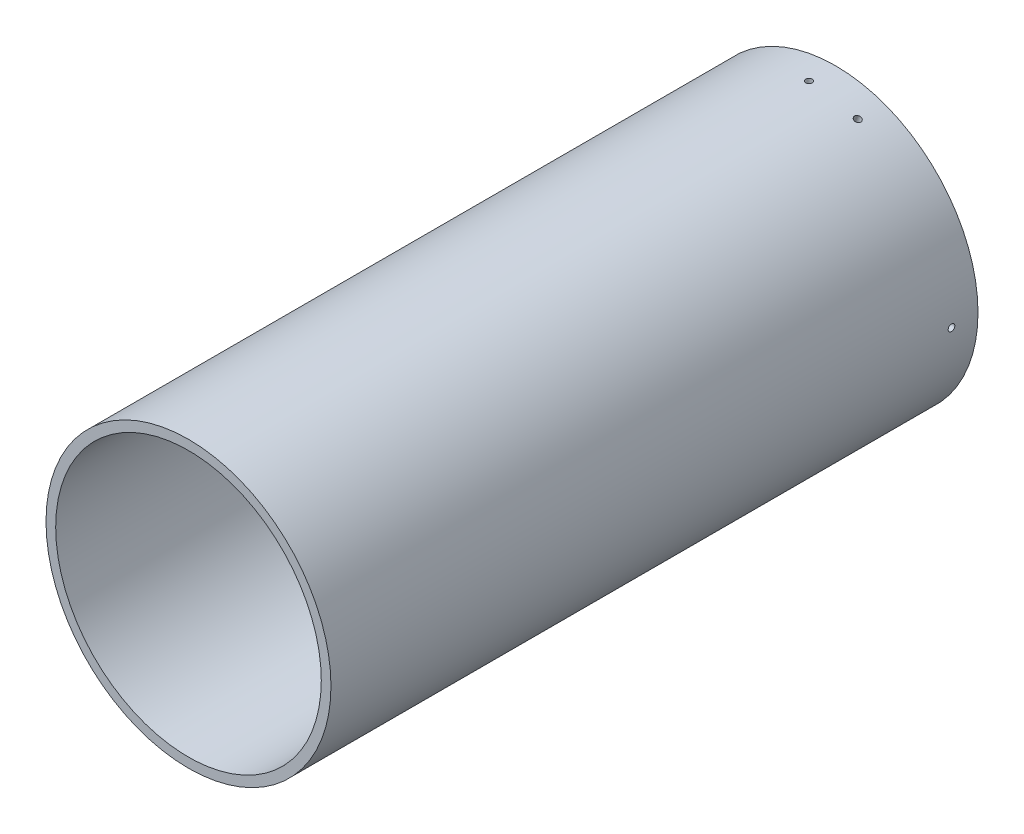
SolidWorks part; units mm, degrees
material "PVC Rigid"
ref_plane "Front Plane" through (0, 0, 0) normal (0, 0, 1) x (1, 0, 0)
ref_plane "Top Plane" through (0, 0, 0) normal (0, 1, 0) x (1, 0, 0)
ref_plane "Right Plane" through (0, 0, 0) normal (1, 0, 0) x (0, 0, -1)
sketch "Sketch1" plane through (0, 0, 0) normal (0, 1, 0) x (1, 0, 0)
  line L0 (0, 0) -> (0, 620)
  dimension "D1" = 620
other "Pipe (standard, s40) P10(1)"
ref_plane "Plane1" through (0, 0, 0) normal (0, 0, -1) x (-1, 0, 0)
sketch "Sketch11" plane through (0, 0, 0) normal (0, 0, -1) x (-1, 0, 0)
  circle A0 centre (0, 0) radius 127.254
  circle A1 centre (0, 0) radius 136.525
  point P3 (0, 0)
  dimension "In_dia" = 254.508
  dimension "Out_dia" = 273.05
sketch "Sketch12" plane through (0, 0, 0) normal (0, 1, 0) x (1, 0, 0)
  line L0 (0, 620) -> (0, 0) construction
  line L1 (136.525, 620) -> (-136.525, 620) construction
  line L2 (127.254, 620) -> (-127.254, 620) construction
  circle A0 centre (0, 594.6) radius 3.175
  dimension "D1" = 6.35
  dimension "D2" = 25.4
extrude "Cut-Extrude1" cut sketch "Sketch12" along normal through all
sketch "Sketch13" plane through (0, 0, 0) normal (0, 1, 0) x (1, 0, 0)
  line L0 (0, 620) -> (0, 0) construction
  line L1 (136.525, 620) -> (-136.525, 620) construction
ref_plane "Plane2" through (0, 0, 0) normal (-0.342, -0.9397, 0) x (0, 0, 1)
sketch "Sketch14" plane through (0, 0, 0) normal (-0.342, -0.9397, 0) x (0, 0, 1)
  line L0 (-620, 0) -> (0, 0) construction
  line L1 (-620, 136.525) -> (-620, -136.525) construction
  circle A0 centre (-594.6, 0) radius 3.175
  dimension "D1" = 6.35
  dimension "D2" = 25.4
extrude "Cut-Extrude2" cut sketch "Sketch14" against normal through all
sketch "Sketch15" plane through (0, 0, 0) normal (1, 0, 0) x (0, 0, -1)
  line L0 (620, 0) -> (0, 0) construction
  line L1 (620, -136.525) -> (620, 136.525) construction
  circle A0 centre (594.6, 0) radius 3.175
  dimension "D1" = 6.35
  dimension "D2" = 25.4
extrude "Cut-Extrude3" cut sketch "Sketch15" along normal through all
